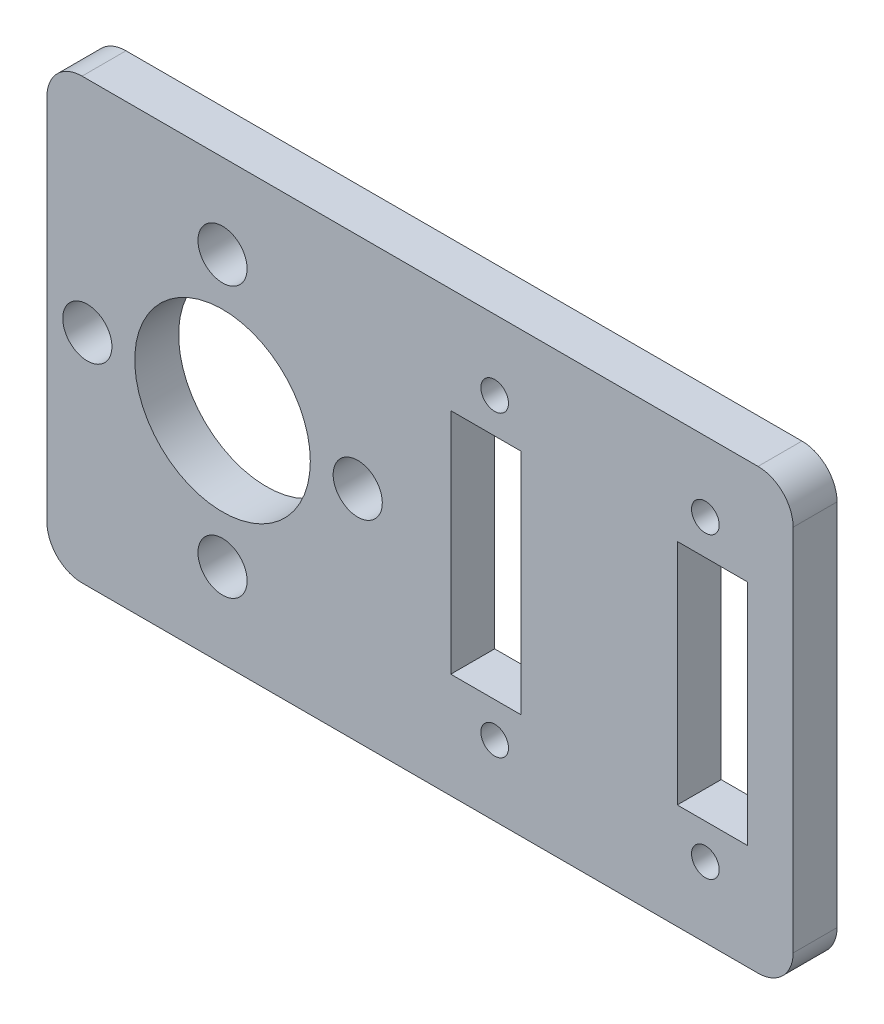
SolidWorks part; units mm, degrees
material "Copper"
ref_plane "Front Plane" through (0, 0, 0) normal (0, 0, 1) x (1, 0, 0)
ref_plane "Top Plane" through (0, 0, 0) normal (0, 1, 0) x (1, 0, 0)
ref_plane "Right Plane" through (0, 0, 0) normal (1, 0, 0) x (0, 0, -1)
sketch "Sketch2" plane through (0, 0, 0) normal (0, 0, 1) x (1, 0, 0)
  line L1 (0, 0) -> (53.975, 0)
  line L2 (0, 0) -> (0, 31.75)
  line L3 (0, 31.75) -> (53.975, 31.75)
  line L4 (53.975, 0) -> (53.975, 31.75)
  line L5 (29.21, 24.13) -> (34.29, 24.13)
  line L6 (29.21, 24.13) -> (29.21, 7.62)
  line L7 (29.21, 7.62) -> (34.29, 7.62)
  line L8 (34.29, 24.13) -> (34.29, 7.62)
  line L9 (45.593, 24.13) -> (50.673, 24.13)
  line L10 (45.593, 24.13) -> (45.593, 7.62)
  line L11 (45.593, 7.62) -> (50.673, 7.62)
  line L12 (50.673, 24.13) -> (50.673, 7.62)
  circle A0 centre (32.385, 26.67) radius 1
  circle A1 centre (47.625, 26.67) radius 1
  circle A2 centre (32.385, 5.08) radius 1
  circle A3 centre (47.625, 5.08) radius 1
  point P17 (31.75, 7.62)
  point P22 (53.975, 15.875)
  dimension "D3" = 15.24
  dimension "D11" = 2
  dimension "D1" = 31.75
  dimension "D2" = 53.975
  dimension "D4" = 15.24
  dimension "D5" = 21.59
  dimension "D6" = 21.59
  dimension "D7" = 5.08
  dimension "D8" = 5.08
  dimension "D9" = 6.35
  dimension "D10" = 6.35
  dimension "D12" = 5.08
  dimension "D13" = 16.51
  dimension "D14" = 22.225
  dimension "D15" = 7.62
  dimension "D16" = 5.08
  dimension "D17" = 16.51
  dimension "D18" = 7.62
  dimension "D19" = 3.302
extrude "Boss-Extrude1" add sketch "Sketch2" along normal blind 3.175
sketch "Sketch3" plane through (0, 0, 3.175) normal (0, 0, 1) x (1, 0, 0)
  line L0 (0, 31.75) -> (0, 0) construction
  line L1 (53.975, 31.75) -> (0, 31.75) construction
  circle A0 centre (12.7, 15.875) radius 6.35
  dimension "D1" = 12.7
  dimension "D2" = 12.7
  dimension "D3" = 15.875
extrude "Cut-Extrude1" cut sketch "Sketch3" against normal blind 3.175
sketch "Sketch4" plane through (0, 0, 3.175) normal (0, 0, 1) x (1, 0, 0)
  line L0 (0, 31.75) -> (0, 0) construction
  circle A0 centre (12.7, 25.654) radius 1.778
  circle A1 centre (12.7, 15.875) radius 6.35 construction
  dimension "D1" = 3.556
  dimension "D2" = 12.7
  dimension "D3" = 9.779
extrude "Cut-Extrude2" cut sketch "Sketch4" against normal blind 3.175
pattern_circular "CirPattern1" count 4 over 360 about axis through (12.7, 15.875, 0) along (0, 0, 1) of "Cut-Extrude2"
fillet "Fillet1" radius 2.54 4 edges at (0, 31.75, 1.5875) (53.975, 31.75, 1.5875) (53.975, 0, 1.5875) (0, 0, 1.5875)
